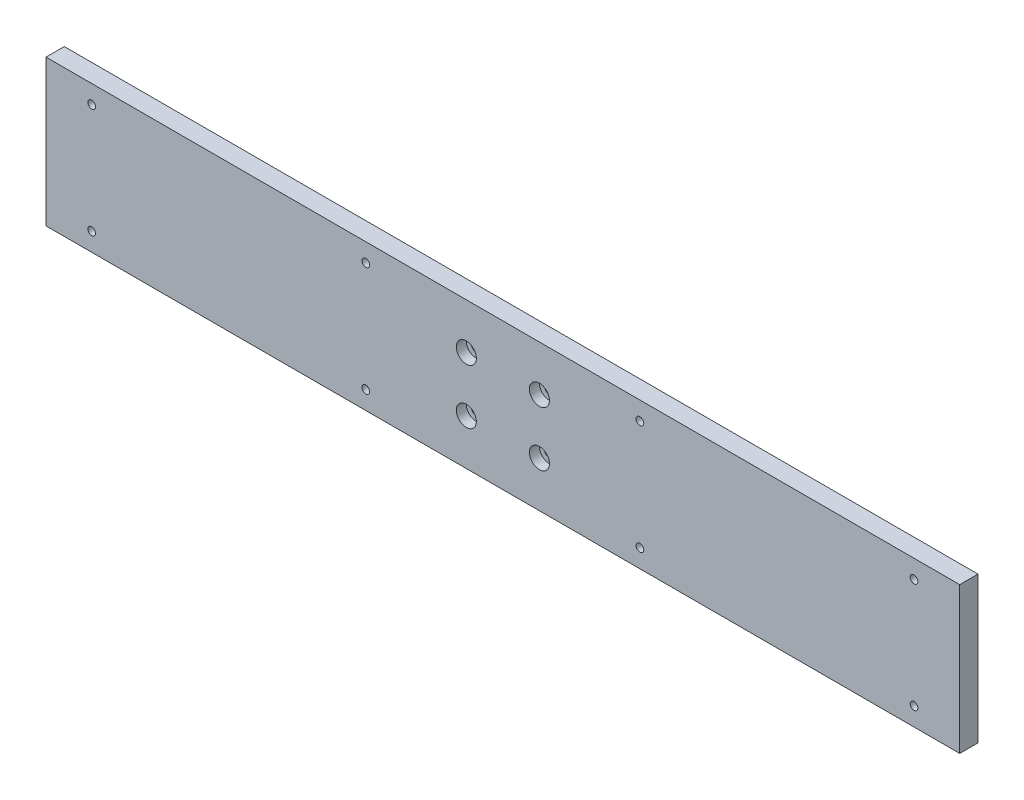
SolidWorks part; units mm, degrees
material "3003 Alloy"
ref_plane "Front Plane" through (0, 0, 0) normal (0, 0, 1) x (1, 0, 0)
ref_plane "Top Plane" through (0, 0, 0) normal (0, 1, 0) x (1, 0, 0)
ref_plane "Right Plane" through (0, 0, 0) normal (1, 0, 0) x (0, 0, -1)
sketch "Sketch1" plane through (0, 0, 0) normal (0, 0, 1) x (1, 0, 0)
  line L1 (-250, -40) -> (250, -40)
  line L2 (-250, -40) -> (-250, 40)
  line L3 (-250, 40) -> (250, 40)
  line L4 (250, -40) -> (250, 40)
  line L5 (-250, -40) -> (250, 40) construction
  line L6 (-250, 40) -> (250, -40) construction
  point P0 (0, 0)
  dimension "D1" = 80
  dimension "D2" = 500
extrude "Boss-Extrude1" add sketch "Sketch1" along normal blind 10
sketch "Sketch2" plane through (0, 0, 10) normal (0, 0, 1) x (1, 0, 0)
  line L0 (-20, 15) -> (20, 15) construction
  line L1 (20, 15) -> (20, -15) construction
  line L2 (20, -15) -> (-20, -15) construction
  line L3 (-20, -15) -> (-20, 15) construction
  circle A0 centre (-20, 15) radius 2.75
  circle A1 centre (20, 15) radius 2.75
  circle A2 centre (20, -15) radius 2.75
  circle A3 centre (-20, -15) radius 2.75
  point P2 (0, 15)
  point P5 (-20, 0)
  dimension "D3" = 5.5
  dimension "D1" = 40
  dimension "D2" = 30
extrude "Cut-Extrude1" cut sketch "Sketch2" against normal through all
sketch "Sketch3" plane through (0, 0, 10) normal (0, 0, 1) x (1, 0, 0)
  circle A0 centre (20, 15) radius 5.5
  circle A1 centre (20, -15) radius 5.5
  circle A2 centre (-20, -15) radius 5.5
  circle A3 centre (-20, 15) radius 5.5
  dimension "D1" = 11
extrude "Cut-Extrude2" cut sketch "Sketch3" against normal blind 5.5
sketch "Sketch4" plane through (0, 0, 10) normal (0, 0, 1) x (1, 0, 0)
  line L0 (-75, 30) -> (75, 30) construction
  line L1 (75, -30) -> (75, 30) construction
  point P0 (-75, 30)
  point P1 (-225, 30)
  point P2 (-225, -30)
  point P3 (-75, -30)
  point P4 (75, -30)
  point P5 (225, -30)
  point P6 (225, 30)
  point P7 (75, 30)
  point P8 (0, 30)
  point P10 (75, 0)
  dimension "D1" = 150
  dimension "D2" = 150
  dimension "D3" = 150
  dimension "D4" = 60
hole_wizard "M5 Tapped Hole1" positions "Sketch5" profile "Sketch6" tap size "M5" standard "ISO"
sketch "Sketch5" plane through (0, 0, 10) normal (0, 0, 1) x (1, 0, 0)
  point P0 (-225, 30)
  point P3 (-225, -30)
  point P6 (-75, -30)
  point P9 (-75, 30)
  point P12 (75, 30)
  point P15 (75, -30)
  point P18 (225, -30)
  point P21 (225, 30)
sketch "Sketch6" plane through (-225, 30, 10) normal (1, 0, 0) x (0, -1, 0)
  line L0 (0, 0) -> (0, 13.6618)
  line L1 (0, 13.6618) -> (2.1, 12.4)
  line L2 (2.1, 12.4) -> (2.1, 0)
  line L5 (2.1, 0) -> (0, 0)
  line L10 (0, 13.6618) -> (-2.1, 12.4) construction
  line L11 (0, -6.35) -> (0, 107.95) construction
  dimension "Tap Drill Dia." = 4.2
  dimension "Tap Drill Depth" = 12.4
  dimension "Drill Angle" = 118
cosmetic thread "Hole Thread1" parameters "D1"=10, "D2"=5
cosmetic thread "Hole Thread2" parameters "D1"=10, "D2"=5
cosmetic thread "Hole Thread3" parameters "D1"=10, "D2"=5
cosmetic thread "Hole Thread4" parameters "D1"=10, "D2"=5
cosmetic thread "Hole Thread5" parameters "D1"=10, "D2"=5
cosmetic thread "Hole Thread6" parameters "D1"=10, "D2"=5
cosmetic thread "Hole Thread7" parameters "D1"=10, "D2"=5
cosmetic thread "Hole Thread8" parameters "D1"=10, "D2"=5
